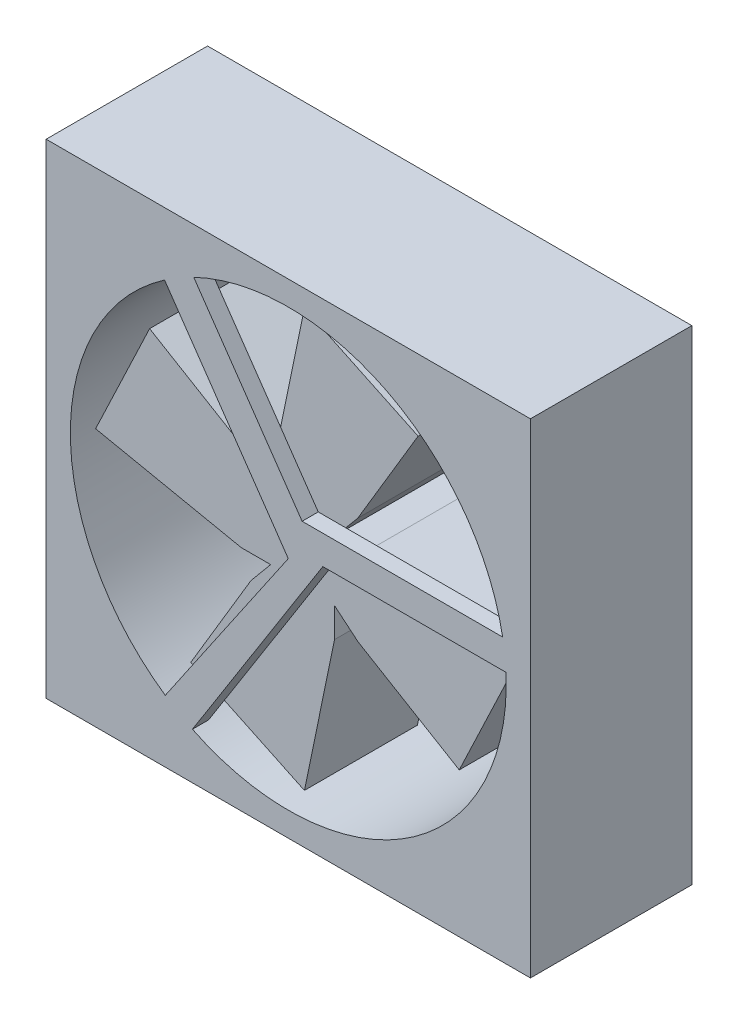
SolidWorks part; units mm, degrees
ref_plane "前视基准面" through (0, 0, 0) normal (0, 0, 1) x (1, 0, 0)
ref_plane "上视基准面" through (0, 0, 0) normal (0, 1, 0) x (1, 0, 0)
ref_plane "右视基准面" through (0, 0, 0) normal (1, 0, 0) x (0, 0, -1)
sketch "草图1" plane through (0, 0, 0) normal (0, 0, 1) x (1, 0, 0)
  line L0 (-40.8227, 46.4926) -> (-10.8227, 46.4926)
  line L1 (-10.8227, 46.4926) -> (-10.8227, 16.4926)
  line L2 (-10.8227, 16.4926) -> (-40.8227, 16.4926)
  line L3 (-40.8227, 16.4926) -> (-40.8227, 46.4926)
  line L4 (-25.8227, 46.4926) -> (-25.8227, 16.4926) construction
  circle A0 centre (-25.8227, 31.4926) radius 13.5
extrude "凸台-拉伸1" add sketch "草图1" along normal blind 10
sketch "草图2" plane through (0, 0, 10) normal (0, 0, 1) x (1, 0, 0)
  line L0 (-32.3978, 44.701) -> (-24.9668, 33.9242)
  line L1 (-24.9668, 33.9242) -> (-11.1164, 33.9242)
  line L2 (-11.1164, 33.9242) -> (-11.1164, 32.1345)
  line L3 (-11.1164, 32.1345) -> (-23.6829, 32.1345)
  line L4 (-23.6829, 32.1345) -> (-32.3978, 18.3619)
  line L5 (-32.3978, 18.3619) -> (-34.0744, 19.4228)
  line L6 (-34.0744, 19.4228) -> (-25.8227, 31.4926)
  line L7 (-25.8227, 31.4926) -> (-34.3731, 43.8928)
  line L8 (-34.3731, 43.8928) -> (-32.5503, 45.1497)
  line L9 (-32.5503, 45.1497) -> (-32.3978, 44.701)
extrude "凸台-拉伸2" add sketch "草图2" against normal blind 1
sketch "草图3" plane through (0, 0, 9) normal (0, 0, -1) x (-1, 0, 0)
  line L0 (25.8227, 44.9926) -> (25.8227, 44.4287) construction
  line L3 (22.5157, 34.819) -> (18.7808, 41.0828)
  line L4 (18.7808, 41.0828) -> (25.8227, 44.4287)
  line L5 (25.8227, 44.4287) -> (27.6902, 35.4026)
  line L6 (27.6902, 35.4026) -> (27.6902, 33.5837)
  line L8 (22.5157, 34.819) -> (23.7315, 33.36)
  line L12 (29.1492, 34.7995) -> (35.413, 38.5345)
  line L13 (35.413, 38.5345) -> (38.7589, 31.4926)
  line L14 (38.7589, 31.4926) -> (29.7327, 29.6251)
  line L15 (29.7327, 29.6251) -> (27.9139, 29.6251)
  line L17 (29.1492, 34.7995) -> (27.6902, 33.5837)
  line L20 (39.3227, 31.4926) -> (38.7589, 31.4926) construction
  line L22 (29.1297, 28.1661) -> (32.8647, 21.9023)
  line L23 (32.8647, 21.9023) -> (25.8227, 18.5564)
  line L24 (25.8227, 18.5564) -> (23.9553, 27.5825)
  line L25 (23.9553, 27.5825) -> (23.9553, 29.4014)
  line L27 (29.1297, 28.1661) -> (27.9139, 29.6251)
  line L30 (25.8227, 17.9926) -> (25.8227, 18.5564) construction
  line L32 (22.4963, 28.1856) -> (16.2325, 24.4506)
  line L33 (16.2325, 24.4506) -> (12.8866, 31.4926)
  line L34 (12.8866, 31.4926) -> (21.9127, 33.36)
  line L35 (21.9127, 33.36) -> (23.7315, 33.36)
  line L37 (22.4963, 28.1856) -> (23.9553, 29.4014)
  line L40 (12.3227, 31.4926) -> (12.8866, 31.4926) construction
  circle A0 centre (25.8227, 31.4926) radius 13.5 construction
  point P43 (25.8227, 31.4926)
  dimension "D1" = 4
extrude "凸台-拉伸3" add sketch "草图3" along normal blind 7
